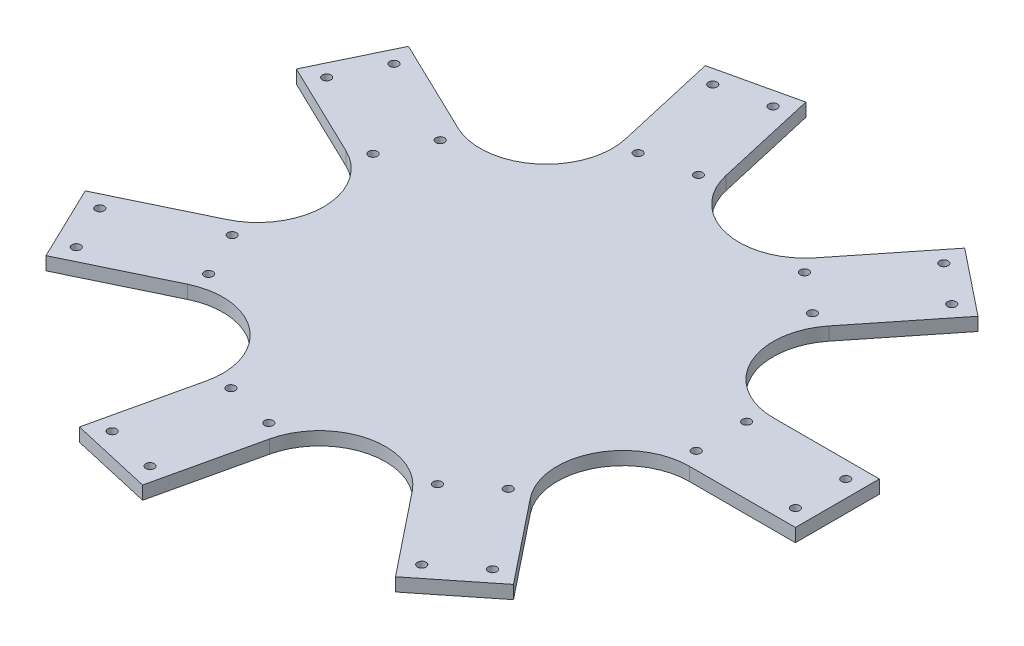
SolidWorks part; units mm, degrees
ref_plane "Front Plane" through (0, 0, 0) normal (0, 0, 1) x (1, 0, 0)
ref_plane "Top Plane" through (0, 0, 0) normal (0, 1, 0) x (1, 0, 0)
ref_plane "Right Plane" through (0, 0, 0) normal (1, 0, 0) x (0, 0, -1)
sketch "Sketch2" plane through (0, 0, 0) normal (0, 0, 1) x (1, 0, 0)
  line L0 (0, 0) -> (0, 63.9226) construction
sketch "Sketch3" plane through (0, 0, 0) normal (0, 1, 0) x (1, 0, 0)
  line L0 (0, 31.75) -> (0, -31.75)
  line L1 (0, 31.75) -> (250, 31.75)
  line L2 (0, -31.75) -> (250, -31.75)
  line L3 (250, 31.75) -> (250, -31.75)
  line L4 (0, 0) -> (-515.3919, 0) construction
  line L5 (237.3, 19.05) -> (237.3, -19.05) construction
  line L6 (237.3, 19.05) -> (162.3, 19.05) construction
  line L7 (162.3, 19.05) -> (162.3, -19.05) construction
  circle A0 centre (162.3, 19.05) radius 3.25
  circle A1 centre (162.3, -19.05) radius 3.25
  circle A2 centre (237.3, 19.05) radius 3.25
  circle A3 centre (237.3, -19.05) radius 3.25
  point P3 (0, 0)
  point P16 (237.3, 0)
  point P17 (162.3, 0)
  dimension "D6" = 6.5
  dimension "D1" = 63.5
  dimension "D2" = 12.7
  dimension "D3" = 250
  dimension "D4" = 75
  dimension "D5" = 12.7
extrude "Boss-Extrude1" add sketch "Sketch3" along normal blind 10
pattern_circular "CirPattern1" count 7 every 51.429 about axis through (0, 0, 0) along (0, 1, 0) of "Boss-Extrude1"
fillet "Fillet1" radius 50 7 edges at (65.9296, 5, 31.75) (16.2833, 5, 71.3416) (-45.6247, 5, 57.2115) (-73.1763, 5, 0) (-45.6247, 5, -57.2115) (16.2833, 5, -71.3416) (65.9296, 5, -31.75)
